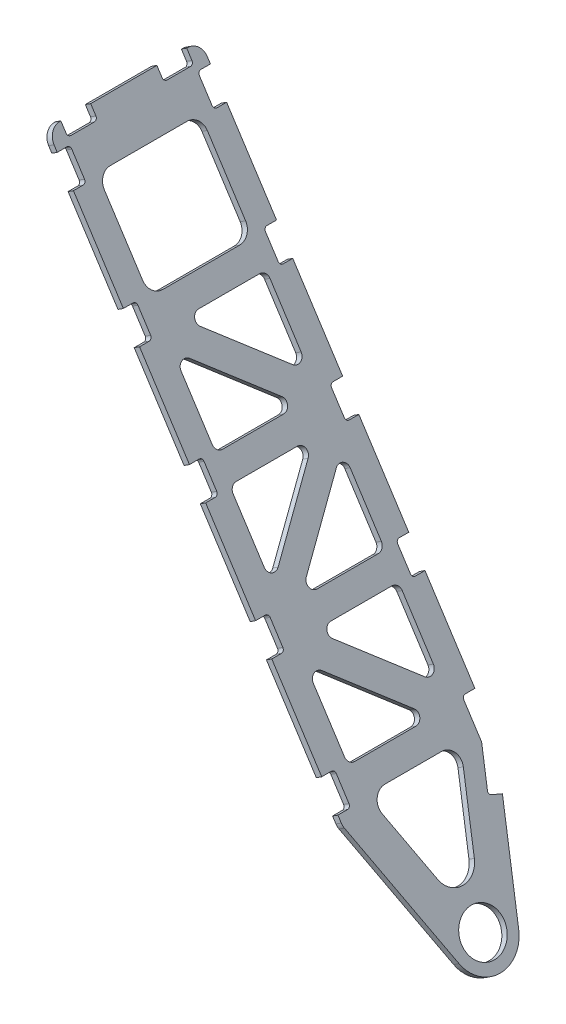
SolidWorks part; units mm, degrees
ref_plane "Front Plane" through (0, 0, 0) normal (0, 0, 1) x (1, 0, 0)
ref_plane "Top Plane" through (0, 0, 0) normal (0, 1, 0) x (1, 0, 0)
ref_plane "Right Plane" through (0, 0, 0) normal (1, 0, 0) x (0, 0, -1)
ref_plane "Plane1" through (106.6039, 69.014, 0) normal (0.8394, 0.5434, 0) x (-0.5434, 0.8394, 0)
sketch "Sketch1" plane through (106.6039, 69.014, 0) normal (0.8394, 0.5434, 0) x (-0.5434, 0.8394, 0)
  line L0 (2192.4569, -117.1428) -> (2192.4569, -136.7008) construction
  line L1 (2133.2749, -136.7008) -> (2133.2749, -117.1428) construction
  line L2 (1951.1569, -117.1428) -> (1951.1569, -136.7008) construction
  line L3 (1891.9749, -136.7008) -> (1891.9749, -117.1428) construction
  line L4 (1709.8569, -117.1428) -> (1709.8569, -136.7008) construction
  line L5 (1650.6749, -136.7008) -> (1650.6749, -117.1428) construction
  line L6 (1468.5569, -117.1428) -> (1468.5569, -136.7008) construction
  line L7 (1317.7529, -109.4514) -> (1324.4422, -91.0729) construction
  line L8 (1409.3749, 148.5412) -> (1409.3749, 168.0992) construction
  line L9 (1468.5569, 168.0992) -> (1468.5569, 148.5412) construction
  line L10 (1650.6749, 148.5412) -> (1650.6749, 168.0992) construction
  line L11 (1709.8569, 168.0992) -> (1709.8569, 148.5412) construction
  line L12 (1891.9749, 148.5412) -> (1891.9749, 168.0992) construction
  line L13 (1951.1569, 168.0992) -> (1951.1569, 148.5412) construction
  line L14 (2133.2749, 148.5412) -> (2133.2749, 168.0992) construction
  line L15 (2374.5749, -136.7008) -> (2374.5749, -117.1428) construction
  line L25 (2433.7569, -117.1428) -> (2433.7569, -136.2008)
  line L26 (2433.7569, -117.1428) -> (2433.7569, -136.7008) construction
  line L27 (2470.3409, -111.3008) -> (2470.3409, -109.1418)
  line L28 (2470.3409, -109.1418) -> (2451.2829, -109.1418)
  line L29 (2444.9329, -102.7918) -> (2444.9329, -56.3098)
  line L30 (2451.2829, -49.9598) -> (2470.3409, -49.9598)
  line L31 (2451.2829, -49.9598) -> (2470.8409, -49.9598) construction
  line L32 (2470.3409, 81.3582) -> (2451.2829, 81.3582)
  line L33 (2444.9329, 87.7082) -> (2444.9329, 134.1902)
  line L34 (2451.2829, 140.5402) -> (2470.3409, 140.5402)
  line L35 (2451.2829, 140.5402) -> (2470.8409, 140.5402) construction
  line L36 (2433.7569, 168.0992) -> (2433.7569, 148.5412) construction
  line L37 (2433.7569, 167.5992) -> (2433.7569, 148.5412)
  line L38 (2427.4069, 142.1912) -> (2380.9249, 142.1912)
  line L39 (2374.5749, 148.5412) -> (2374.5749, 167.5992)
  line L40 (2374.5749, 148.5412) -> (2374.5749, 168.0992) construction
  line L41 (2192.4569, 167.5992) -> (2192.4569, 148.5412)
  line L42 (2186.1069, 142.1912) -> (2139.6249, 142.1912)
  line L43 (2133.2749, 148.5412) -> (2133.2749, 167.5992)
  line L44 (1891.9749, 167.5992) -> (1709.8569, 167.5992)
  line L45 (1951.1569, 167.5992) -> (1951.1569, 148.5412)
  line L46 (1944.8069, 142.1912) -> (1898.3249, 142.1912)
  line L47 (1891.9749, 148.5412) -> (1891.9749, 167.5992)
  line L48 (1650.6749, 167.5992) -> (1468.5569, 167.5992)
  line L49 (1709.8569, 167.5992) -> (1709.8569, 148.5412)
  line L50 (1703.5069, 142.1912) -> (1657.0249, 142.1912)
  line L51 (1650.6749, 148.5412) -> (1650.6749, 167.5992)
  line L52 (1397.0986, 167.5992) -> (1409.3749, 167.5992)
  line L53 (1468.5569, 167.5992) -> (1468.5569, 148.5412)
  line L54 (1462.2069, 142.1912) -> (1415.7249, 142.1912)
  line L55 (1409.3749, 148.5412) -> (1409.3749, 167.5992)
  line L56 (1138.0186, -43.5014) -> (1317.9239, -108.9816)
  line L57 (1468.5569, -136.2008) -> (1650.6749, -136.2008)
  line L58 (1709.8569, -136.2008) -> (1891.9749, -136.2008)
  line L59 (1317.9239, -108.9816) -> (1324.4422, -91.0729)
  line L60 (1332.581, -87.2777) -> (1396.136, -110.4098)
  line L61 (1398.3078, -110.7928) -> (1462.2069, -110.7928)
  line L62 (1468.5569, -117.1428) -> (1468.5569, -136.2008)
  line L63 (1951.1569, -136.2008) -> (2133.2749, -136.2008)
  line L64 (1650.6749, -136.2008) -> (1650.6749, -117.1428)
  line L65 (1657.0249, -110.7928) -> (1703.5069, -110.7928)
  line L66 (1709.8569, -117.1428) -> (1709.8569, -136.2008)
  line L68 (1891.9749, -136.2008) -> (1891.9749, -117.1428)
  line L69 (1898.3249, -110.7928) -> (1944.8069, -110.7928)
  line L70 (1951.1569, -117.1428) -> (1951.1569, -136.2008)
  line L72 (2133.2749, -136.2008) -> (2133.2749, -117.1428)
  line L73 (2139.6249, -110.7928) -> (2186.1069, -110.7928)
  line L74 (2192.4569, -117.1428) -> (2192.4569, -136.2008)
  line L76 (2374.5749, -136.2008) -> (2374.5749, -117.1428)
  line L77 (2380.9249, -110.7928) -> (2427.4069, -110.7928)
  line L78 (2001.4671, -64.1727) -> (2115.136, 57.074)
  line L79 (2137.9659, 48.046) -> (2137.9659, -73.2008)
  line L80 (2124.7659, -86.4008) -> (2011.097, -86.4008)
  line L81 (1873.836, -25.6756) -> (1760.1671, 95.5712)
  line L82 (1769.797, 117.7992) -> (1883.4659, 117.7992)
  line L83 (1896.6659, 104.5992) -> (1896.6659, -16.6476)
  line L84 (1959.6659, 117.7992) -> (2073.3347, 117.7992)
  line L85 (2082.9646, 95.5712) -> (1969.2958, -25.6756)
  line L86 (1946.4659, -16.6476) -> (1946.4659, 104.5992)
  line L87 (1518.8671, -64.1727) -> (1632.536, 57.074)
  line L88 (1655.3659, 48.046) -> (1655.3659, -73.2008)
  line L89 (1642.1659, -86.4008) -> (1528.497, -86.4008)
  line L90 (1832.0347, -86.4008) -> (1718.3659, -86.4008)
  line L91 (1705.1659, -73.2008) -> (1705.1659, 48.046)
  line L92 (1727.9958, 57.074) -> (1841.6646, -64.1727)
  line L93 (1477.0659, 117.7992) -> (1590.7347, 117.7992)
  line L94 (1600.3646, 95.5712) -> (1486.6958, -25.6756)
  line L95 (1463.8659, -16.6476) -> (1463.8659, 104.5992)
  line L96 (2379.2659, 91.8992) -> (2379.2659, -60.5008)
  line L97 (2353.3659, -86.4008) -> (2213.6659, -86.4008)
  line L98 (2187.7659, -60.5008) -> (2187.7659, 91.8992)
  line L99 (2213.6659, 117.7992) -> (2353.3659, 117.7992)
  line L100 (1414.0659, 71.8727) -> (1414.0659, -40.4742)
  line L101 (1379.3076, -64.8123) -> (1257.7609, -20.5729)
  line L102 (1257.7609, 51.9714) -> (1379.3076, 96.2108)
  line L120 (2445.4409, -136.2008) -> (2433.7569, -136.2008)
  line L121 (2470.8409, -109.1418) -> (2451.2829, -109.1418) construction
  line L122 (2470.8409, 81.3582) -> (2451.2829, 81.3582) construction
  line L123 (2445.4409, 167.5992) -> (2433.7569, 167.5992)
  line L124 (2470.3409, 81.3582) -> (2470.3409, -49.9598)
  line L125 (2470.3409, 142.6992) -> (2470.3409, 140.5402)
  line L126 (2192.4569, 168.0992) -> (2192.4569, 148.5412) construction
  line L128 (2192.4569, 167.5992) -> (2374.5749, 167.5992)
  line L141 (2133.2749, 167.5992) -> (1951.1569, 167.5992)
  line L155 (1388.5823, 166.0976) -> (1138.0186, 74.8999)
  line L156 (2192.4569, -136.2008) -> (2374.5749, -136.2008)
  line L158 (2374.0749, -136.2008) -> (2374.0749, -117.1428) construction
  line L159 (2380.9249, -110.2928) -> (2427.4069, -110.2928) construction
  line L160 (2434.2569, -117.1428) -> (2434.2569, -136.2008) construction
  line L161 (2192.9569, -136.2008) -> (2374.0749, -136.2008) construction
  line L162 (2434.2569, -136.2008) -> (2445.4409, -136.2008) construction
  line L163 (2433.7569, -136.7008) -> (2445.4409, -136.7008) construction
  line L164 (2470.8409, -111.3008) -> (2470.8409, -109.1418) construction
  line L165 (2470.3409, -111.3008) -> (2470.3409, -109.6418) construction
  line L166 (2470.3409, -109.6418) -> (2451.2829, -109.6418) construction
  line L167 (2444.4329, -102.7918) -> (2444.4329, -56.3098) construction
  line L168 (2451.2829, -49.4598) -> (2470.3409, -49.4598) construction
  line L169 (2470.3409, -49.4598) -> (2470.3409, 80.8582) construction
  line L170 (2470.8409, -49.9598) -> (2470.8409, 81.3582) construction
  line L171 (2470.3409, 80.8582) -> (2451.2829, 80.8582) construction
  line L172 (2444.4329, 87.7082) -> (2444.4329, 134.1902) construction
  line L173 (2470.3409, 141.0402) -> (2470.3409, 142.6992) construction
  line L174 (2451.2829, 141.0402) -> (2470.3409, 141.0402) construction
  line L175 (2470.8409, 140.5402) -> (2470.8409, 142.6992) construction
  line L176 (2445.4409, 168.0992) -> (2433.7569, 168.0992) construction
  line L177 (2445.4409, 167.5992) -> (2434.2569, 167.5992) construction
  line L178 (2434.2569, 167.5992) -> (2434.2569, 148.5412) construction
  line L179 (2427.4069, 141.6912) -> (2380.9249, 141.6912) construction
  line L180 (2374.0749, 167.5992) -> (2192.9569, 167.5992) construction
  line L181 (2374.5749, 168.0992) -> (2192.4569, 168.0992) construction
  line L182 (2374.0749, 148.5412) -> (2374.0749, 167.5992) construction
  line L183 (2192.9569, 167.5992) -> (2192.9569, 148.5412) construction
  line L184 (2186.1069, 141.6912) -> (2139.6249, 141.6912) construction
  line L187 (2132.7749, 148.5412) -> (2132.7749, 167.5992) construction
  line L188 (2132.7749, 167.5992) -> (1951.6569, 167.5992) construction
  line L189 (2133.2749, 168.0992) -> (1951.1569, 168.0992) construction
  line L190 (1951.6569, 167.5992) -> (1951.6569, 148.5412) construction
  line L191 (1944.8069, 141.6912) -> (1898.3249, 141.6912) construction
  line L192 (1891.4749, 148.5412) -> (1891.4749, 167.5992) construction
  line L193 (1891.4749, 167.5992) -> (1710.3569, 167.5992) construction
  line L194 (1891.9749, 168.0992) -> (1709.8569, 168.0992) construction
  line L195 (1710.3569, 167.5992) -> (1710.3569, 148.5412) construction
  line L196 (1703.5069, 141.6912) -> (1657.0249, 141.6912) construction
  line L197 (1650.1749, 148.5412) -> (1650.1749, 167.5992) construction
  line L198 (1650.1749, 167.5992) -> (1469.0569, 167.5992) construction
  line L199 (1650.6749, 168.0992) -> (1468.5569, 168.0992) construction
  line L200 (1469.0569, 167.5992) -> (1469.0569, 148.5412) construction
  line L201 (1462.2069, 141.6912) -> (1415.7249, 141.6912) construction
  line L202 (1408.8749, 148.5412) -> (1408.8749, 167.5992) construction
  line L203 (1408.8749, 167.5992) -> (1397.0986, 167.5992) construction
  line L204 (1409.3749, 168.0992) -> (1397.0986, 168.0992) construction
  line L205 (1388.4113, 166.5674) -> (1137.8476, 75.3697) construction
  line L206 (1137.8476, -43.9712) -> (1317.7529, -109.4514) construction
  line L207 (1138.0186, -43.5014) -> (1317.4541, -108.8106) construction
  line L208 (1317.4541, -108.8106) -> (1323.9723, -90.9019) construction
  line L209 (1332.7521, -86.8079) -> (1396.307, -109.94) construction
  line L210 (1398.3078, -110.2928) -> (1462.2069, -110.2928) construction
  line L211 (1469.0569, -136.2008) -> (1650.1749, -136.2008) construction
  line L212 (1468.5569, -136.7008) -> (1650.6749, -136.7008) construction
  line L213 (1469.0569, -117.1428) -> (1469.0569, -136.2008) construction
  line L214 (1650.1749, -136.2008) -> (1650.1749, -117.1428) construction
  line L215 (1657.0249, -110.2928) -> (1703.5069, -110.2928) construction
  line L216 (1710.3569, -136.2008) -> (1891.4749, -136.2008) construction
  line L217 (1709.8569, -136.7008) -> (1891.9749, -136.7008) construction
  line L218 (1710.3569, -117.1428) -> (1710.3569, -136.2008) construction
  line L219 (1891.4749, -136.2008) -> (1891.4749, -117.1428) construction
  line L220 (1898.3249, -110.2928) -> (1944.8069, -110.2928) construction
  line L221 (1951.6569, -136.2008) -> (2132.7749, -136.2008) construction
  line L222 (1951.1569, -136.7008) -> (2133.2749, -136.7008) construction
  line L223 (1951.6569, -117.1428) -> (1951.6569, -136.2008) construction
  line L224 (2132.7749, -136.2008) -> (2132.7749, -117.1428) construction
  line L225 (2139.6249, -110.2928) -> (2186.1069, -110.2928) construction
  line L226 (2192.9569, -117.1428) -> (2192.9569, -136.2008) construction
  line L227 (2192.4569, -136.7008) -> (2374.5749, -136.7008) construction
  circle A0 centre (1159.5659, 15.6992) radius 42.291
  arc A27 (2451.2829, -109.1418) -> (2444.9329, -102.7918) centre (2451.2829, -102.7918) cw
  arc A28 (2444.9329, -56.3098) -> (2451.2829, -49.9598) centre (2451.2829, -56.3098) cw
  arc A29 (2451.2829, 81.3582) -> (2444.9329, 87.7082) centre (2451.2829, 87.7082) cw
  arc A30 (2444.9329, 134.1902) -> (2451.2829, 140.5402) centre (2451.2829, 134.1902) cw
  arc A32 (2433.7569, 148.5412) -> (2427.4069, 142.1912) centre (2427.4069, 148.5412) cw
  arc A33 (2380.9249, 142.1912) -> (2374.5749, 148.5412) centre (2380.9249, 148.5412) cw
  arc A34 (2192.4569, 148.5412) -> (2186.1069, 142.1912) centre (2186.1069, 148.5412) cw
  arc A35 (2139.6249, 142.1912) -> (2133.2749, 148.5412) centre (2139.6249, 148.5412) cw
  arc A36 (1951.1569, 148.5412) -> (1944.8069, 142.1912) centre (1944.8069, 148.5412) cw
  arc A37 (1898.3249, 142.1912) -> (1891.9749, 148.5412) centre (1898.3249, 148.5412) cw
  arc A38 (1709.8569, 148.5412) -> (1703.5069, 142.1912) centre (1703.5069, 148.5412) cw
  arc A39 (1657.0249, 142.1912) -> (1650.6749, 148.5412) centre (1657.0249, 148.5412) cw
  arc A40 (1468.5569, 148.5412) -> (1462.2069, 142.1912) centre (1462.2069, 148.5412) cw
  arc A41 (1415.7249, 142.1912) -> (1409.3749, 148.5412) centre (1415.7249, 148.5412) cw
  arc A44 (1324.4422, -91.0729) -> (1332.581, -87.2777) centre (1330.4092, -93.2448) cw
  arc A45 (1396.136, -110.4098) -> (1398.3078, -110.7928) centre (1398.3078, -104.4428) ccw
  arc A46 (1462.2069, -110.7928) -> (1468.5569, -117.1428) centre (1462.2069, -117.1428) cw
  arc A47 (1650.6749, -117.1428) -> (1657.0249, -110.7928) centre (1657.0249, -117.1428) cw
  arc A48 (1703.5069, -110.7928) -> (1709.8569, -117.1428) centre (1703.5069, -117.1428) cw
  arc A49 (1891.9749, -117.1428) -> (1898.3249, -110.7928) centre (1898.3249, -117.1428) cw
  arc A50 (1944.8069, -110.7928) -> (1951.1569, -117.1428) centre (1944.8069, -117.1428) cw
  arc A51 (2133.2749, -117.1428) -> (2139.6249, -110.7928) centre (2139.6249, -117.1428) cw
  arc A52 (2186.1069, -110.7928) -> (2192.4569, -117.1428) centre (2186.1069, -117.1428) cw
  arc A53 (2374.5749, -117.1428) -> (2380.9249, -110.7928) centre (2380.9249, -117.1428) cw
  arc A54 (2427.4069, -110.7928) -> (2433.7569, -117.1428) centre (2427.4069, -117.1428) cw
  arc A55 (2115.136, 57.074) -> (2137.9659, 48.046) centre (2124.7659, 48.046) cw
  arc A56 (2137.9659, -73.2008) -> (2124.7659, -86.4008) centre (2124.7659, -73.2008) cw
  arc A57 (2011.097, -86.4008) -> (2001.4671, -64.1727) centre (2011.097, -73.2008) cw
  arc A58 (1760.1671, 95.5712) -> (1769.797, 117.7992) centre (1769.797, 104.5992) cw
  arc A59 (1883.4659, 117.7992) -> (1896.6659, 104.5992) centre (1883.4659, 104.5992) cw
  arc A60 (1896.6659, -16.6476) -> (1873.836, -25.6756) centre (1883.4659, -16.6476) cw
  arc A61 (2073.3347, 117.7992) -> (2082.9646, 95.5712) centre (2073.3347, 104.5992) cw
  arc A62 (1969.2958, -25.6756) -> (1946.4659, -16.6476) centre (1959.6659, -16.6476) cw
  arc A63 (1946.4659, 104.5992) -> (1959.6659, 117.7992) centre (1959.6659, 104.5992) cw
  arc A64 (1632.536, 57.074) -> (1655.3659, 48.046) centre (1642.1659, 48.046) cw
  arc A65 (1655.3659, -73.2008) -> (1642.1659, -86.4008) centre (1642.1659, -73.2008) cw
  arc A66 (1528.497, -86.4008) -> (1518.8671, -64.1727) centre (1528.497, -73.2008) cw
  arc A67 (1718.3659, -86.4008) -> (1705.1659, -73.2008) centre (1718.3659, -73.2008) cw
  arc A68 (1705.1659, 48.046) -> (1727.9958, 57.074) centre (1718.3659, 48.046) cw
  arc A69 (1841.6646, -64.1727) -> (1832.0347, -86.4008) centre (1832.0347, -73.2008) cw
  arc A70 (1590.7347, 117.7992) -> (1600.3646, 95.5712) centre (1590.7347, 104.5992) cw
  arc A71 (1486.6958, -25.6756) -> (1463.8659, -16.6476) centre (1477.0659, -16.6476) cw
  arc A72 (1463.8659, 104.5992) -> (1477.0659, 117.7992) centre (1477.0659, 104.5992) cw
  arc A73 (2379.2659, -60.5008) -> (2353.3659, -86.4008) centre (2353.3659, -60.5008) cw
  arc A74 (2213.6659, -86.4008) -> (2187.7659, -60.5008) centre (2213.6659, -60.5008) cw
  arc A75 (2187.7659, 91.8992) -> (2213.6659, 117.7992) centre (2213.6659, 91.8992) cw
  arc A76 (2353.3659, 117.7992) -> (2379.2659, 91.8992) centre (2353.3659, 91.8992) cw
  arc A77 (1414.0659, -40.4742) -> (1379.3076, -64.8123) centre (1388.1659, -40.4742) cw
  arc A78 (1257.7609, -20.5729) -> (1257.7609, 51.9714) centre (1270.9628, 15.6992) cw
  arc A79 (1379.3076, 96.2108) -> (1414.0659, 71.8727) centre (1388.1659, 71.8727) cw
  arc A92 (2445.4409, -136.2008) -> (2470.3409, -111.3008) centre (2445.4409, -111.3008) ccw
  arc A97 (2470.3409, 142.6992) -> (2445.4409, 167.5992) centre (2445.4409, 142.6992) ccw
  arc A108 (1397.0986, 167.5992) -> (1388.5823, 166.0976) centre (1397.0986, 142.6992) ccw
  arc A109 (1138.0186, 74.8999) -> (1138.0186, -43.5014) centre (1159.5659, 15.6992) ccw
  arc A111 (2374.0749, -117.1428) -> (2380.9249, -110.2928) centre (2380.9249, -117.1428) cw construction
  arc A112 (2427.4069, -110.2928) -> (2434.2569, -117.1428) centre (2427.4069, -117.1428) cw construction
  arc A113 (2445.4409, -136.7008) -> (2470.8409, -111.3008) centre (2445.4409, -111.3008) ccw construction
  arc A114 (2451.2829, -109.6418) -> (2444.4329, -102.7918) centre (2451.2829, -102.7918) cw construction
  arc A115 (2444.4329, -56.3098) -> (2451.2829, -49.4598) centre (2451.2829, -56.3098) cw construction
  arc A116 (2451.2829, 80.8582) -> (2444.4329, 87.7082) centre (2451.2829, 87.7082) cw construction
  arc A117 (2444.4329, 134.1902) -> (2451.2829, 141.0402) centre (2451.2829, 134.1902) cw construction
  arc A118 (2470.8409, 142.6992) -> (2445.4409, 168.0992) centre (2445.4409, 142.6992) ccw construction
  arc A119 (2434.2569, 148.5412) -> (2427.4069, 141.6912) centre (2427.4069, 148.5412) cw construction
  arc A120 (2380.9249, 141.6912) -> (2374.0749, 148.5412) centre (2380.9249, 148.5412) cw construction
  arc A121 (2192.9569, 148.5412) -> (2186.1069, 141.6912) centre (2186.1069, 148.5412) cw construction
  arc A122 (2139.6249, 141.6912) -> (2132.7749, 148.5412) centre (2139.6249, 148.5412) cw construction
  arc A123 (1951.6569, 148.5412) -> (1944.8069, 141.6912) centre (1944.8069, 148.5412) cw construction
  arc A124 (1898.3249, 141.6912) -> (1891.4749, 148.5412) centre (1898.3249, 148.5412) cw construction
  arc A125 (1710.3569, 148.5412) -> (1703.5069, 141.6912) centre (1703.5069, 148.5412) cw construction
  arc A126 (1657.0249, 141.6912) -> (1650.1749, 148.5412) centre (1657.0249, 148.5412) cw construction
  arc A127 (1469.0569, 148.5412) -> (1462.2069, 141.6912) centre (1462.2069, 148.5412) cw construction
  arc A128 (1415.7249, 141.6912) -> (1408.8749, 148.5412) centre (1415.7249, 148.5412) cw construction
  arc A129 (1397.0986, 168.0992) -> (1388.4113, 166.5674) centre (1397.0986, 142.6992) ccw construction
  arc A130 (1137.8476, 75.3697) -> (1137.8476, -43.9712) centre (1159.5659, 15.6992) ccw construction
  arc A131 (1323.9723, -90.9019) -> (1332.7521, -86.8079) centre (1330.4092, -93.2448) cw construction
  arc A132 (1396.307, -109.94) -> (1398.3078, -110.2928) centre (1398.3078, -104.4428) ccw construction
  arc A133 (1462.2069, -110.2928) -> (1469.0569, -117.1428) centre (1462.2069, -117.1428) cw construction
  arc A134 (1650.1749, -117.1428) -> (1657.0249, -110.2928) centre (1657.0249, -117.1428) cw construction
  arc A135 (1703.5069, -110.2928) -> (1710.3569, -117.1428) centre (1703.5069, -117.1428) cw construction
  arc A136 (1891.4749, -117.1428) -> (1898.3249, -110.2928) centre (1898.3249, -117.1428) cw construction
  arc A137 (1944.8069, -110.2928) -> (1951.6569, -117.1428) centre (1944.8069, -117.1428) cw construction
  arc A138 (2132.7749, -117.1428) -> (2139.6249, -110.2928) centre (2139.6249, -117.1428) cw construction
  arc A139 (2186.1069, -110.2928) -> (2192.9569, -117.1428) centre (2186.1069, -117.1428) cw construction
extrude "Boss-Extrude1" add sketch "Sketch1" against normal blind 12.7
